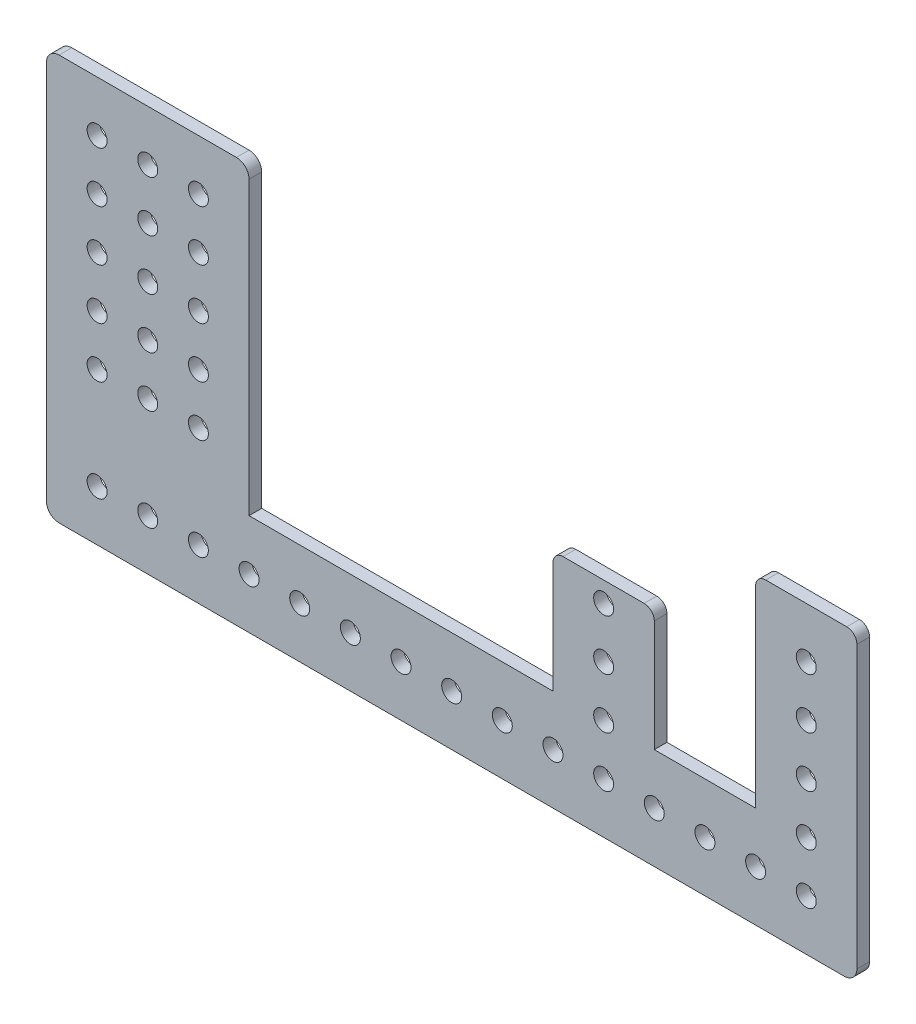
SolidWorks part; units mm, degrees
ref_plane "Front Plane" through (0, 0, 0) normal (0, 0, 1) x (1, 0, 0)
ref_plane "Top Plane" through (0, 0, 0) normal (0, 1, 0) x (1, 0, 0)
ref_plane "Right Plane" through (0, 0, 0) normal (1, 0, 0) x (0, 0, -1)
sketch "Sketch1" plane through (0, 0, 0) normal (0, 0, 1) x (1, 0, 0)
  line L0 (99.0226, -20.0767) -> (102.1976, -20.0767)
  line L1 (-101.0024, -20.0767) -> (99.0226, -20.0767)
  line L2 (-101.0024, -20.0767) -> (-101.0024, -42.3017)
  line L3 (-97.8274, -45.4767) -> (99.0226, -45.4767)
  line L4 (102.1976, 2.1483) -> (102.1976, -42.3017)
  line L6 (-101.0024, -20.0767) -> (-101.0024, 52.9483)
  line L7 (-97.8274, 56.1233) -> (-53.3774, 56.1233)
  line L8 (-50.2024, -20.0767) -> (-50.2024, 52.9483)
  line L9 (102.1976, -20.0767) -> (102.1976, 2.1483)
  arc A0 (-101.0024, -42.3017) -> (-97.8274, -45.4767) centre (-97.8274, -42.3017) ccw
  arc A1 (99.0226, -45.4767) -> (102.1976, -42.3017) centre (99.0226, -42.3017) ccw
  arc A3 (-53.3774, 56.1233) -> (-50.2024, 52.9483) centre (-53.3774, 52.9483) cw
  arc A4 (-101.0024, 52.9483) -> (-97.8274, 56.1233) centre (-97.8274, 52.9483) cw
  point P11 (-101.0024, -45.4767)
  point P14 (102.1976, -45.4767)
  point P17 (102.1976, -20.0767)
  point P20 (-50.2024, 56.1233)
  point P23 (-101.0024, 56.1233)
  dimension "D5" = 3.175
  dimension "D1" = 25.4
  dimension "D2" = 203.2
  dimension "D3" = 50.8
  dimension "D4" = 76.2
extrude "Boss-Extrude1" add sketch "Sketch1" along normal blind 3.175 contours L1 L8 L7 L6 | L4 L1 L2 L3
sketch "Sketch3" plane through (0, 0, 3.175) normal (0, 0, 1) x (1, 0, 0)
  line L0 (-50.2024, -20.0767) -> (102.1976, -20.0767) construction
  line L1 (48.8576, 10.4033) -> (28.5376, 10.4033)
  line L2 (51.3976, 7.8633) -> (51.3976, -20.0767)
  line L3 (51.3976, -20.0767) -> (25.9976, -20.0767)
  line L4 (25.9976, 7.8633) -> (25.9976, -20.0767)
  line L6 (79.3376, 30.7233) -> (99.6576, 30.7233)
  line L7 (76.7976, 28.1833) -> (76.7976, -20.0767)
  line L8 (76.7976, -20.0767) -> (102.1976, -20.0767)
  line L9 (102.1976, 28.1833) -> (102.1976, -20.0767)
  line L10 (-50.2024, -20.0767) -> (-50.2024, 52.9483) construction
  arc A0 (99.6576, 30.7233) -> (102.1976, 28.1833) centre (99.6576, 28.1833) cw
  arc A1 (79.3376, 30.7233) -> (76.7976, 28.1833) centre (79.3376, 28.1833) ccw
  arc A2 (28.5376, 10.4033) -> (25.9976, 7.8633) centre (28.5376, 7.8633) ccw
  arc A3 (48.8576, 10.4033) -> (51.3976, 7.8633) centre (48.8576, 7.8633) cw
  point P14 (102.1976, 30.7233)
  point P17 (76.7976, 30.7233)
  point P20 (25.9976, 10.4033)
  point P23 (51.3976, 10.4033)
  dimension "D7" = 2.54
  dimension "D1" = 30.48
  dimension "D2" = 76.2
  dimension "D3" = 25.4
  dimension "D4" = 25.4
  dimension "D5" = 25.4
  dimension "D6" = 50.8
extrude "Boss-Extrude2" add sketch "Sketch3" against normal up to surface (3.175 mm away) up to face at (-24.8024, 0.2433, 0)
sketch "Sketch4" plane through (0, 0, 3.175) normal (0, 0, 1) x (1, 0, 0)
  line L0 (-101.0024, -42.3017) -> (-101.0024, 52.9483) construction
  line L1 (-97.8274, -45.4767) -> (99.0226, -45.4767) construction
  line L3 (102.1976, 28.1833) -> (102.1976, -42.3017) construction
  line L4 (-97.8274, 56.1233) -> (-53.3774, 56.1233) construction
  line L5 (76.7976, 28.1833) -> (76.7976, -20.0767) construction
  line L6 (-50.2024, -20.0767) -> (-50.2024, 52.9483) construction
  circle A0 centre (-88.3024, -32.7767) radius 2.5
  circle A1 centre (-75.6024, -32.7767) radius 2.5
  circle A2 centre (-62.9024, -32.7767) radius 2.5
  circle A3 centre (-50.2024, -32.7767) radius 2.5
  circle A4 centre (-37.5024, -32.7767) radius 2.5
  circle A5 centre (-24.8024, -32.7767) radius 2.5
  circle A6 centre (-12.1024, -32.7767) radius 2.5
  circle A7 centre (0.5976, -32.7767) radius 2.5
  circle A8 centre (13.2976, -32.7767) radius 2.5
  circle A9 centre (25.9976, -32.7767) radius 2.5
  circle A10 centre (38.6976, -32.7767) radius 2.5
  circle A11 centre (51.3976, -32.7767) radius 2.5
  circle A12 centre (64.0976, -32.7767) radius 2.5
  circle A13 centre (76.7976, -32.7767) radius 2.5
  circle A14 centre (89.4976, -32.7767) radius 2.5
  circle A15 centre (38.6976, -20.0767) radius 2.5
  circle A16 centre (89.4976, -20.0767) radius 2.5
  circle A17 centre (-88.3024, 43.4233) radius 2.5
  circle A19 centre (-62.9024, 43.4233) radius 2.5
  circle A21 centre (-62.9024, 30.7233) radius 2.5
  circle A23 centre (-62.9024, 18.0233) radius 2.5
  circle A25 centre (-62.9024, 5.3233) radius 2.5
  circle A27 centre (-62.9024, -7.3767) radius 2.5
  circle A30 centre (-88.3024, 30.7233) radius 2.5
  circle A31 centre (-88.3024, 18.0233) radius 2.5
  circle A32 centre (-88.3024, 5.3233) radius 2.5
  circle A33 centre (-88.3024, -7.3767) radius 2.5
  circle A36 centre (38.6976, -7.3767) radius 2.5
  circle A37 centre (89.4976, -7.3767) radius 2.5
  circle A39 centre (38.6976, 5.3233) radius 2.5
  circle A40 centre (89.4976, 5.3233) radius 2.5
  circle A44 centre (-88.3024, 56.1233) radius 2.5 [skipped]
  circle A45 centre (-88.3024, 68.8233) radius 2.5 [skipped]
  circle A46 centre (89.4976, 18.0233) radius 2.5
  circle A47 centre (-75.6024, 43.4233) radius 2.5 [skipped]
  circle A48 centre (-75.6024, 30.7233) radius 2.5 [skipped]
  circle A49 centre (-75.6024, 18.0233) radius 2.5 [skipped]
  circle A50 centre (-75.6024, 5.3233) radius 2.5 [skipped]
  circle A51 centre (-75.6024, -7.3767) radius 2.5 [skipped]
  circle A52 centre (-75.6024, -20.0767) radius 2.5 [skipped]
  circle A53 centre (-62.9024, -20.0767) radius 2.5 [skipped]
  circle A54 centre (-88.3024, -20.0767) radius 2.5 [skipped]
  circle A55 centre (-75.6024, 43.4233) radius 2.5
  circle A56 centre (-75.6024, 30.7233) radius 2.5
  circle A57 centre (-75.6024, 18.0233) radius 2.5
  circle A58 centre (-75.6024, 5.3233) radius 2.5
  circle A59 centre (-75.6024, -7.3767) radius 2.5
  dimension "D1" = 5
  dimension "D5" = 12.7
  dimension "D8" = 5
  dimension "D11" = 5
  dimension "D17" = 5
  dimension "D7" = 5
  dimension "D2" = 12.7
  dimension "D3" = 12.7
  dimension "D6" = 25.4
  dimension "D9" = 12.7
  dimension "D10" = 25.4
  dimension "D12" = 12.7
  dimension "D13" = 12.7
  dimension "D18" = 12.7
  dimension "D19" = 12.7
  dimension "D4" = 15
  dimension "D14" = 3
  dimension "D15" = 6
  dimension "D16" = 3
  dimension "D20" = 5
extrude "Cut-Extrude1" cut sketch "Sketch4" against normal through all
